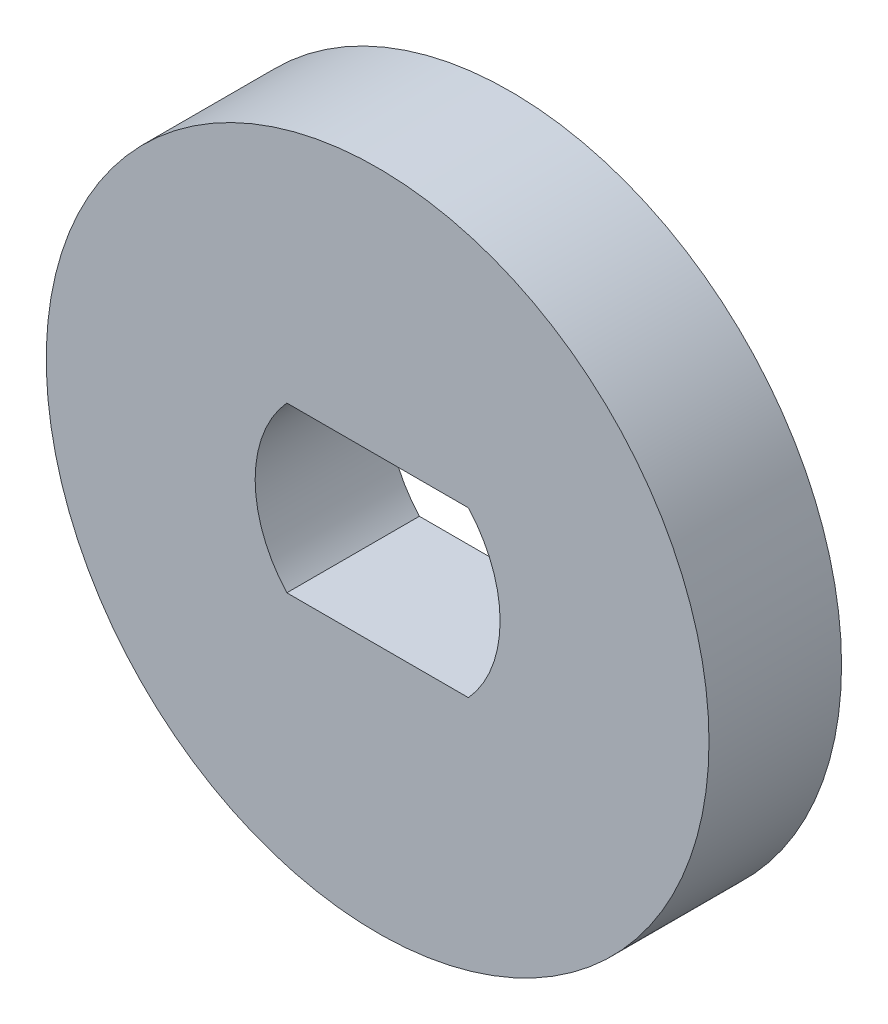
SolidWorks part; units mm, degrees
ref_plane "Front Plane" through (0, 0, 0) normal (0, 0, 1) x (1, 0, 0)
ref_plane "Top Plane" through (0, 0, 0) normal (0, 1, 0) x (1, 0, 0)
ref_plane "Right Plane" through (0, 0, 0) normal (1, 0, 0) x (0, 0, -1)
sketch "Sketch1" plane through (0, 0, 0) normal (0, 0, 1) x (1, 0, 0)
  line L1 (-2.1752, 1.9685) -> (2.1752, 1.9685)
  line L2 (-2.1752, 1.9685) -> (-2.1752, -1.9685)
  line L3 (-2.1752, -1.9685) -> (2.1752, -1.9685)
  line L4 (2.1752, 1.9685) -> (2.1752, -1.9685)
  circle A0 centre (0, 0) radius 7.9375
  arc A1 (2.1752, -1.9685) -> (2.1752, 1.9685) centre (0, 0) ccw
  arc A2 (-2.1752, 1.9685) -> (-2.1752, -1.9685) centre (0, 0) ccw
  dimension "D1" = 15.875
  dimension "D2" = 2.9337
  dimension "D3" = 3.937
extrude "Boss-Extrude1" add sketch "Sketch1" along normal blind 3.175 contours A0 A2 L1 A1 L3
